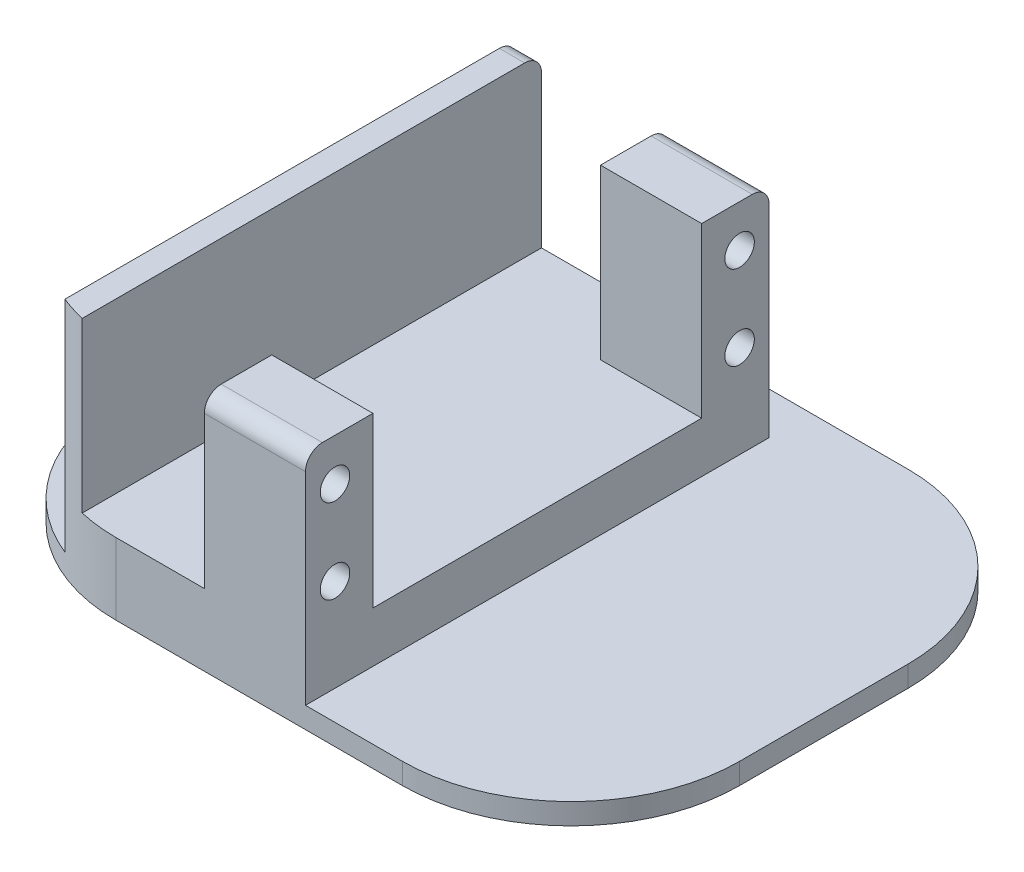
SolidWorks part; units mm, degrees
ref_plane "Plan de face" through (0, 0, 0) normal (0, 0, 1) x (1, 0, 0)
ref_plane "Plan de dessus" through (0, 0, 0) normal (0, 1, 0) x (1, 0, 0)
ref_plane "Plan de droite" through (0, 0, 0) normal (1, 0, 0) x (0, 0, -1)
sketch "Esquisse1" plane through (0, 0, 0) normal (0, 1, 0) x (1, 0, 0)
  line L1 (0, 0) -> (74, 0)
  line L2 (0, 0) -> (0, 60)
  line L3 (0, 60) -> (74, 60)
  line L4 (74, 0) -> (74, 60)
  dimension "D1" = 60
  dimension "D2" = 74
extrude "Boss.-Extru.1" add sketch "Esquisse1" along normal blind 2.5
sketch "Esquisse2" plane through (0, 2.5, 0) normal (0, 1, 0) x (1, 0, 0)
  line L0 (74, 60) -> (0, 60) construction
  line L1 (12.5, 55) -> (42.5, 55)
  line L2 (12.5, 55) -> (12.5, 0)
  line L3 (12.5, 0) -> (42.5, 0)
  line L4 (42.5, 55) -> (42.5, 0)
  line L6 (0, 60) -> (0, 0) construction
  dimension "D1" = 30
  dimension "D2" = 55
  dimension "D3" = 5
  dimension "D4" = 12.5
extrude "Boss.-Extru.2" add sketch "Esquisse2" along normal blind 6
sketch "Esquisse4" plane through (0, 8.5, 0) normal (0, 1, 0) x (1, 0, 0)
  line L0 (42.5, 0) -> (42.5, 55) construction
  line L1 (42.5, 55) -> (30.5, 55)
  line L2 (42.5, 55) -> (42.5, 47)
  line L3 (42.5, 47) -> (30.5, 47)
  line L4 (12.5, 55) -> (12.5, 52)
  line L5 (12.5, 55) -> (12.5, 0) construction
  line L7 (12.5, 0) -> (15.5, 0)
  line L8 (12.5, 0) -> (12.5, 13)
  line L9 (30.5, 8) -> (42.5, 8)
  line L10 (42.5, 0) -> (42.5, 8)
  line L11 (42.5, 55) -> (12.5, 55) construction
  line L12 (42.5, 0) -> (42.5, 55) construction
  line L13 (15.5, 55) -> (12.5, 55)
  line L14 (12.5, 52) -> (12.5, 13)
  line L15 (30.5, 0) -> (42.5, 0)
  line L16 (15.5, 52) -> (15.5, 13)
  line L17 (15.5, 52) -> (15.5, 55)
  line L19 (30.5, 47) -> (30.5, 55)
  line L20 (15.5, 13) -> (15.5, 0)
  line L22 (30.5, 8) -> (30.5, 0)
  dimension "D1" = 8
  dimension "D2" = 8
  dimension "D3" = 27
  dimension "D4" = 15
  dimension "D5" = 15
extrude "Boss.-Extru.3" add sketch "Esquisse4" along normal blind 20
sketch "Esquisse5" plane through (42.5, 0, 0) normal (1, 0, 0) x (0, 0, -1)
  line L0 (55, 28.5) -> (55, 2.5) construction
  line L1 (0, 28.5) -> (0, 2.5) construction
  line L3 (8, 8.5) -> (47, 8.5) construction
  circle A0 centre (3.5, 23.5) radius 1.75
  circle A1 centre (3.5, 13.5) radius 1.75
  circle A2 centre (51.5, 23.5) radius 1.75
  circle A3 centre (51.5, 13.5) radius 1.75
  point P8 (55, 15.5)
  dimension "D1" = 3.5
  dimension "D2" = 3.5
  dimension "D3" = 3.5
  dimension "D4" = 3.5
  dimension "D5" = 3.5
  dimension "D6" = 3.5
  dimension "D7" = 3.5
  dimension "D8" = 3.5
  dimension "D9" = 3.5
  dimension "D10" = 5
  dimension "D11" = 10
  dimension "D12" = 10
  dimension "D13" = 5
  dimension "D14" = 5
extrude "Enlèv. mat.-Extru.1" cut sketch "Esquisse5" against normal blind 20
sketch "Esquisse6" plane through (12.5, 0, 0) normal (-1, 0, 0) x (0, 0, 1)
  line L0 (-55, 28.5) -> (0, 28.5) construction
  line L1 (0, 28.5) -> (0, 2.5) construction
  circle A0 centre (-18, 18.5) radius 2.95
  dimension "D1" = 5.9
  dimension "D2" = 10
  dimension "D3" = 18
extrude "Boss.-Extru.4" add sketch "Esquisse6" along normal blind 5
fillet "Congé1" radius 1 1 edges at (12.5, 18.5, -20.95)
fillet "Congé2" radius 20 4 edges at (74, 1.25, -60) (74, 1.25, 0) (0, 1.25, 0) (0, 1.25, -60)
fillet "Congé3" radius 2 3 edges at (36.5, 28.5, 0) (14, 28.5, -55) (36.5, 28.5, -55)
